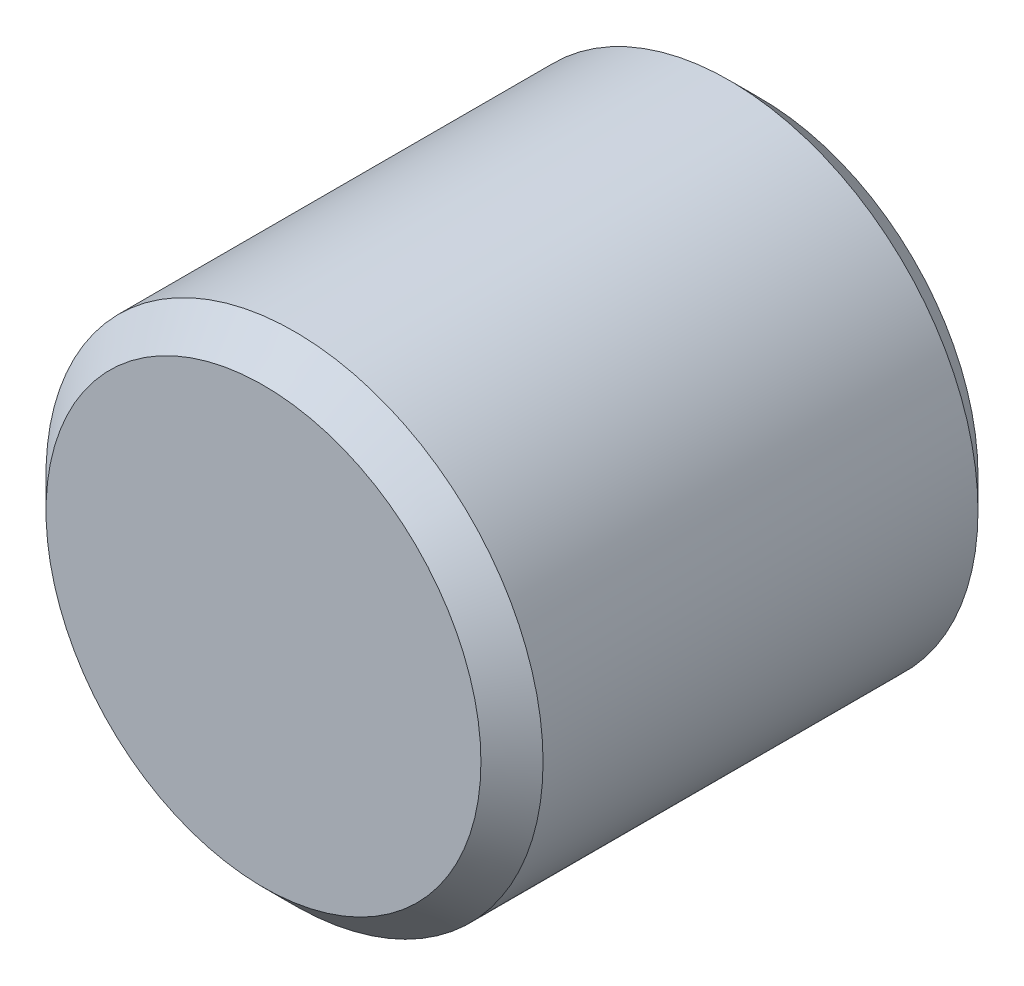
SolidWorks part; units mm, degrees
ref_plane "Front Plane" through (0, 0, 0) normal (0, 0, 1) x (1, 0, 0)
ref_plane "Top Plane" through (0, 0, 0) normal (0, 1, 0) x (1, 0, 0)
ref_plane "Right Plane" through (0, 0, 0) normal (1, 0, 0) x (0, 0, -1)
sketch "Sketch1" plane through (0, 0, 0) normal (0, 0, 1) x (1, 0, 0)
  circle A0 centre (0, 0) radius 2
  dimension "D1" = 4
extrude "Boss-Extrude1" add sketch "Sketch1" along normal blind 4
chamfer "Chamfer1" distance 0.25 angle 45 2 edges at (2, 0, 0) (2, 0, 4)
